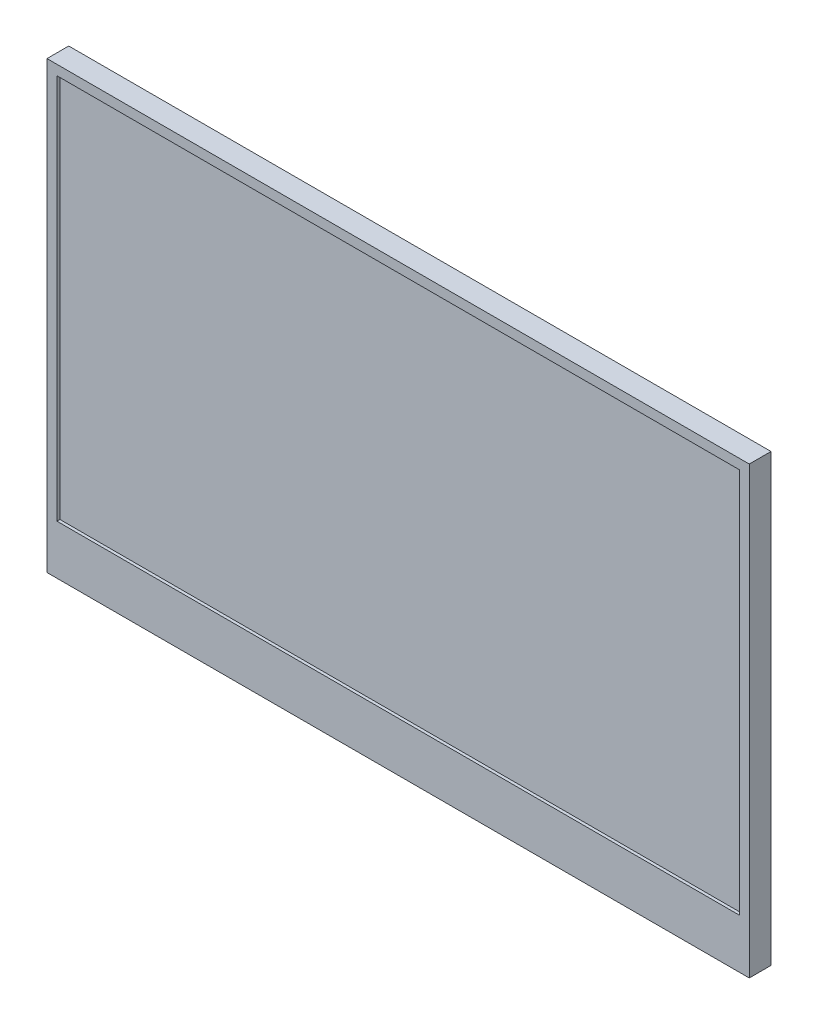
SolidWorks part; units mm, degrees
ref_plane "정면" through (0, 0, 0) normal (0, 0, 1) x (1, 0, 0)
ref_plane "윗면" through (0, 0, 0) normal (0, 1, 0) x (1, 0, 0)
ref_plane "우측면" through (0, 0, 0) normal (1, 0, 0) x (0, 0, -1)
sketch "스케치2" plane through (0, 0, 0) normal (0, 0, 1) x (1, 0, 0)
  line L1 (-177.5, -112.5) -> (177.5, -112.5)
  line L2 (-177.5, -112.5) -> (-177.5, 112.5)
  line L3 (-177.5, 112.5) -> (177.5, 112.5)
  line L4 (177.5, -112.5) -> (177.5, 112.5)
  line L5 (-177.5, -112.5) -> (177.5, 112.5) construction
  line L6 (-177.5, 112.5) -> (177.5, -112.5) construction
  point P0 (0, 0)
  dimension "D1" = 355
  dimension "D2" = 225
extrude "보스-돌출2" add sketch "스케치2" along normal blind 11
sketch "스케치4" plane through (0, 0, 11) normal (0, 0, 1) x (1, 0, 0)
  line L0 (-177.5, 112.5) -> (-177.5, -112.5) construction
  line L1 (-172.5, 107.5) -> (172.5, 107.5)
  line L2 (-172.5, 107.5) -> (-172.5, -87.5)
  line L3 (-172.5, -87.5) -> (172.5, -87.5)
  line L4 (172.5, 107.5) -> (172.5, -87.5)
  line L5 (-177.5, -112.5) -> (177.5, -112.5) construction
  dimension "D1" = 345
  dimension "D2" = 195
  dimension "D3" = 5
  dimension "D4" = 25
extrude "컷-돌출2" cut sketch "스케치4" against normal blind 1.5
